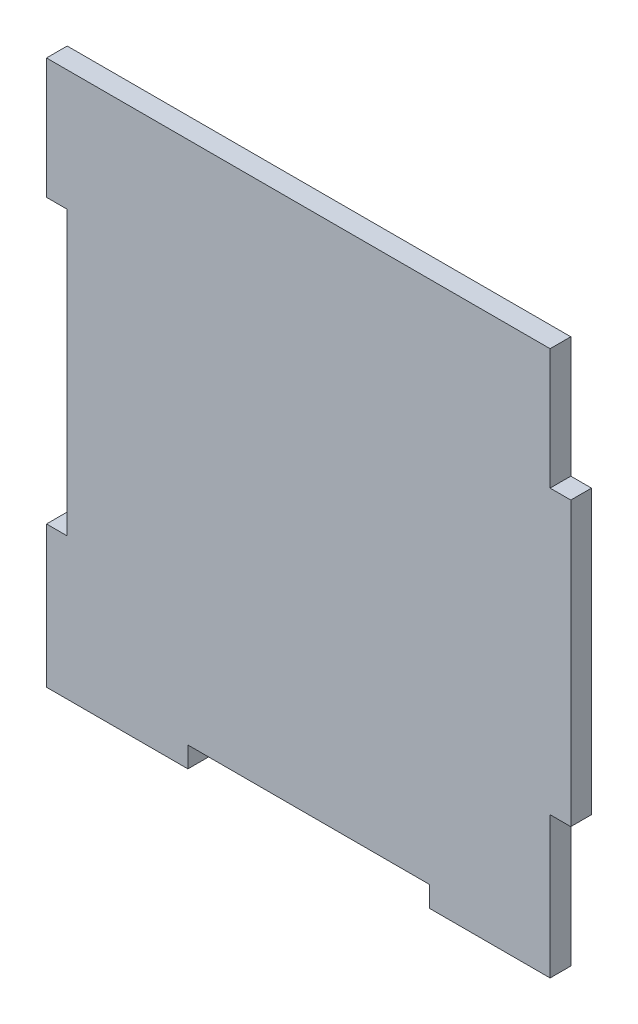
SolidWorks part; units mm, degrees
ref_plane "Front Plane" through (0, 0, 0) normal (0, 0, 1) x (1, 0, 0)
ref_plane "Top Plane" through (0, 0, 0) normal (0, 1, 0) x (1, 0, 0)
ref_plane "Right Plane" through (0, 0, 0) normal (1, 0, 0) x (0, 0, -1)
sketch "Sketch1" plane through (0, 0, 0) normal (0, 0, 1) x (1, 0, 0)
  line L0 (0, 35) -> (0, -38) construction
  line L5 (-35, 38) -> (-17.5, 38)
  line L6 (-35, 20.5) -> (-35, -20.5)
  line L7 (-17.5, -38) -> (17.5, -38)
  line L24 (35, 38) -> (35, 20.5)
  line L25 (-35, 38) -> (35, -38) construction
  line L26 (-35, -38) -> (35, 38) construction
  line L27 (-35, 0) -> (35, 0) construction
  line L31 (-35, -20.5) -> (-38, -20.5)
  line L32 (-35, 20.5) -> (-38, 20.5)
  line L33 (-38, 20.5) -> (-38, 38)
  line L34 (-38, 38) -> (-35, 38)
  line L35 (-38, -20.5) -> (-38, -38)
  line L36 (-17.5, 38) -> (17.5, 38)
  line L37 (35, -38) -> (35, -41)
  line L38 (35, -20.5) -> (38, -20.5)
  line L39 (35, -41) -> (17.5, -41)
  line L40 (35, 20.5) -> (38, 20.5)
  line L41 (17.5, -41) -> (17.5, -38)
  line L42 (-17.5, -38) -> (-17.5, -41)
  line L43 (38, 20.5) -> (38, -20.5)
  line L45 (-35, -41) -> (-17.5, -41)
  line L46 (17.5, 38) -> (35, 38)
  line L47 (35, -20.5) -> (35, -38)
  line L48 (-38, -38) -> (-38, -41)
  line L49 (-38, -41) -> (-35, -41)
  point P0 (0, 0)
  dimension "D1" = 76
  dimension "D2" = 70
  dimension "D3" = 17.5
  dimension "D4" = 17.5
  dimension "D5" = 3
  dimension "D6" = 3
  dimension "D7" = 3
extrude "Boss-Extrude1" add sketch "Sketch1" along normal blind 3
